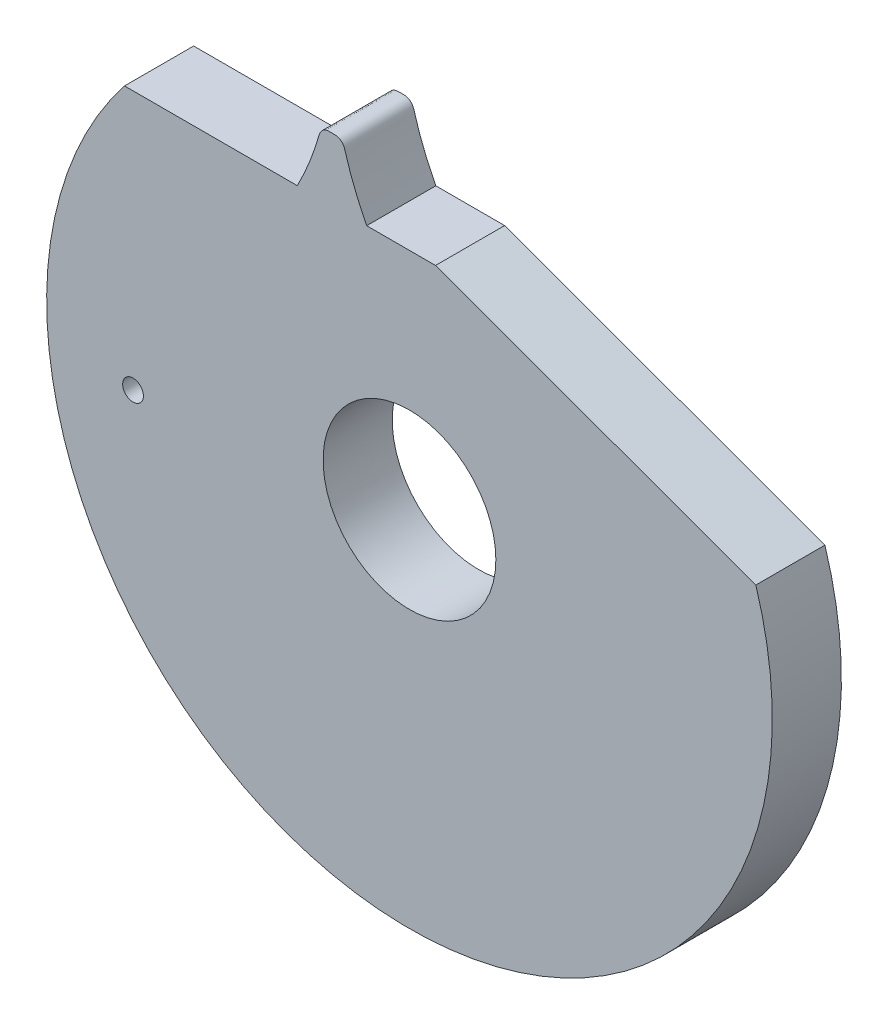
SolidWorks part; units mm, degrees
ref_plane "Front Plane" through (0, 0, 0) normal (0, 0, 1) x (1, 0, 0)
ref_plane "Top Plane" through (0, 0, 0) normal (0, 1, 0) x (1, 0, 0)
ref_plane "Right Plane" through (0, 0, 0) normal (1, 0, 0) x (0, 0, -1)
sketch "Croquis1" plane through (0, 0, 0) normal (0, 0, 1) x (1, 0, 0)
  line L0 (-2.0616, 1.625) -> (-0.8116, 1.625)
  line L1 (0, -2.625) -> (0, 1.375) construction
  line L2 (-0.3096, 1.625) -> (0.1884, 1.625)
  line L4 (0.1884, 1.625) -> (2.506, 0.7815)
  arc A0 (-2.0616, 1.625) -> (2.506, 0.7815) centre (0, 0) ccw
  circle A1 centre (0, 0) radius 0.625
  circle A2 centre (-2, -0.25) radius 0.075
  spline S0 degree 3 poles (-0.8116, 1.625) (-0.7988, 1.65) (-0.7825, 1.6831) (-0.7633, 1.7244) (-0.7527, 1.7481) (-0.7426, 1.7712) (-0.7331, 1.7938) (-0.724, 1.8158) (-0.7155, 1.8373) (-0.7075, 1.8582) (-0.6999, 1.8785) (-0.6928, 1.8983) (-0.6862, 1.9174) (-0.68, 1.936) (-0.6742, 1.954) (-0.6688, 1.9714) (-0.6634, 1.9898) (-0.6593, 2.0038) (-0.6567, 2.0136) (-0.6555, 2.0177) (-0.6542, 2.0217) (-0.6528, 2.0257) (-0.6513, 2.0296) (-0.6495, 2.0336) (-0.6476, 2.0377) (-0.6454, 2.0418) (-0.6428, 2.046) (-0.6399, 2.0504) (-0.6363, 2.0549) (-0.6321, 2.0596) (-0.6269, 2.0644) (-0.6205, 2.0691) (-0.6128, 2.0735) (-0.6038, 2.0771) (-0.5939, 2.0794) (-0.5793, 2.0803) (-0.5606, 2.0796) (-0.5418, 2.0803) (-0.5272, 2.0794) (-0.5173, 2.0771) (-0.5083, 2.0735) (-0.5006, 2.0691) (-0.4943, 2.0644) (-0.4891, 2.0596) (-0.4848, 2.0549) (-0.4812, 2.0504) (-0.4783, 2.046) (-0.4757, 2.0418) (-0.4735, 2.0377) (-0.4716, 2.0336) (-0.4699, 2.0296) (-0.4683, 2.0257) (-0.4669, 2.0217) (-0.4656, 2.0177) (-0.4644, 2.0136) (-0.4618, 2.0038) (-0.4577, 1.9898) (-0.4523, 1.9714) (-0.4469, 1.954) (-0.4411, 1.936) (-0.4349, 1.9174) (-0.4283, 1.8983) (-0.4212, 1.8785) (-0.4136, 1.8582) (-0.4056, 1.8373) (-0.3971, 1.8158) (-0.3881, 1.7938) (-0.3785, 1.7712) (-0.3684, 1.7481) (-0.3578, 1.7244) (-0.3386, 1.6831) (-0.3223, 1.65) (-0.3096, 1.625) knots 0 0 0 0 0.076643 0.100908 0.124531 0.147511 0.16985 0.191547 0.212603 0.233016 0.252788 0.271918 0.290406 0.308252 0.325457 0.342019 0.35794 0.377966 0.381853 0.385707 0.389546 0.393393 0.397276 0.401231 0.405299 0.409534 0.414002 0.418784 0.423978 0.4297 0.436077 0.443235 0.451262 0.460162 0.469799 0.478976 0.5 0.521024 0.530201 0.539838 0.548738 0.556765 0.563923 0.5703 0.576022 0.581216 0.585998 0.590466 0.594701 0.598769 0.602724 0.606607 0.610454 0.614293 0.618147 0.622034 0.64206 0.657981 0.674543 0.691748 0.709594 0.728082 0.747212 0.766984 0.787397 0.808453 0.83015 0.852489 0.875469 0.899092 0.923357 1 1 1 1
  point P84 (-0.8116, 1.625)
  dimension "D1" = 5.25
  dimension "D5" = 1.25
  dimension "D6" = 0.15
  dimension "D3" = 2.25
  dimension "D4" = 4.25
  dimension "D7" = 0.25
  dimension "D8" = 2
  dimension "D9" = 20
extrude "Saliente-Extruir1" add sketch "Croquis1" along normal blind 0.5
